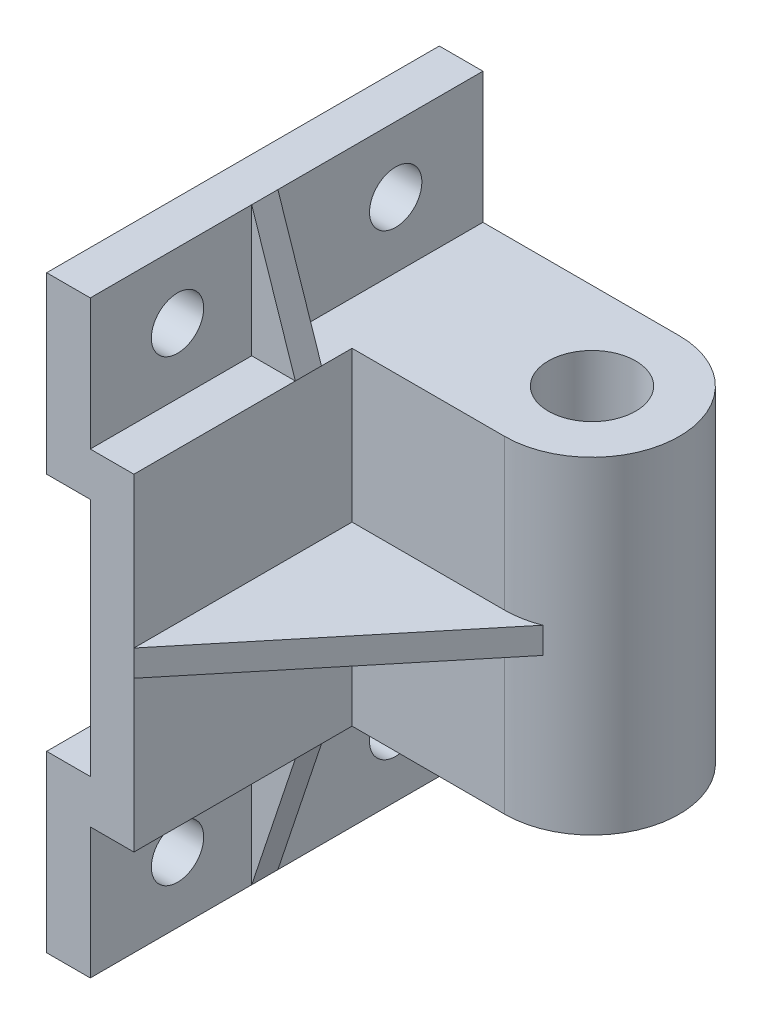
SolidWorks part; units mm, degrees
ref_plane "Ön Düzlem" through (0, 0, 0) normal (0, 0, 1) x (1, 0, 0)
ref_plane "Üst Düzlem" through (0, 0, 0) normal (0, 1, 0) x (1, 0, 0)
ref_plane "Sağ Düzlem" through (0, 0, 0) normal (1, 0, 0) x (0, 0, -1)
sketch "Çizim1" plane through (0, 0, 0) normal (0, 0, 1) x (1, 0, 0)
  line L2 (0, 0) -> (0, -75)
  line L4 (-10, -10) -> (-10, -65)
  line L7 (-10, -10) -> (-20, -10)
  line L9 (0, 0) -> (-10, 0)
  line L12 (-20, -10) -> (-20, 30)
  line L13 (-20, 30) -> (-10, 30)
  line L14 (-10, 0) -> (-10, 30)
  line L15 (-10, -65) -> (-20, -65)
  line L17 (0, -75) -> (-10, -75)
  line L20 (-20, -65) -> (-20, -105)
  line L21 (-20, -105) -> (-10, -105)
  line L22 (-10, -75) -> (-10, -105)
  point P0 (0, 0)
  point P2 (0, 0)
  point P8 (-40.7042, 0)
  point P12 (0, 0)
  point P13 (0, 0)
  point P18 (0, 0)
  point P19 (0, 0)
  point P20 (0, 0)
  point P21 (-10, 22.0605)
  point P22 (-20, -105.2649)
  dimension "D1" = 10
  dimension "D2" = 10
  dimension "D3" = 10
  dimension "D4" = 10
  dimension "D5" = 10
  dimension "D6" = 55
  dimension "D7" = 75
  dimension "D8" = 10
  dimension "D9" = 135
  dimension "D10" = 30
extrude "Yükseklik-Ekstrüzyon1" add sketch "Çizim1" against normal mid plane 90
sketch "Çizim2" plane through (0, 0, 0) normal (0, 1, 0) x (1, 0, 0)
  line L0 (0, 25) -> (35, 25) construction
  line L1 (0, 45) -> (35, 45)
  line L2 (0, 5) -> (35, 5)
  line L3 (-10, 45) -> (-10, -45) construction
  line L6 (0, 45) -> (0, -45) construction
  line L7 (0, 45) -> (0, 5)
  arc A1 (35, 5) -> (35, 45) centre (35, 25) ccw
  point P2 (18.7078, 23.4413)
  point P9 (0, 0)
  point P12 (35, 23.4413)
  point P13 (11.0631, 23.4413)
  point P14 (0, 0)
  point P15 (0, 25)
  point P16 (0, 0)
  point P17 (35, 3.4413)
  point P18 (35, 43.4413)
  point P19 (0, 39.2754)
  point P20 (0, 0)
  dimension "D2" = 20
  dimension "D1" = 45
  dimension "D3" = 40
extrude "Yükseklik-Ekstrüzyon2" add sketch "Çizim2" against normal up to surface (75 mm away) up to face at (-5, -75, 0)
sketch "Çizim3" plane through (0, 0, 0) normal (0, 1, 0) x (1, 0, 0)
  circle A0 centre (35, 25) radius 10
  dimension "D1" = 20
extrude "Kes-Ekstrüzyon1" cut sketch "Çizim3" against normal blind 75
sketch "Çizim4" plane through (-10, 0, 0) normal (1, 0, 0) x (0, 0, -1)
  line L0 (-45, 0) -> (-45, 30) construction
  line L1 (45, 0) -> (-45, 0) construction
  circle A0 centre (-25, 15) radius 6
  circle A1 centre (25, 15) radius 6
  point P6 (-25, 14.0431)
  point P9 (0, 0)
  dimension "D3" = 12
  dimension "D4" = 12
  dimension "D1" = 20
  dimension "D2" = 50
  dimension "D5" = 15
extrude "Kes-Ekstrüzyon2" cut sketch "Çizim4" against normal through all
ref_plane "Düzlem1" through (0, -37.5, 0) normal (0, 1, 0) x (1, 0, 0)
mirror "Aynalama1" about plane through (0, -37.5, 0) normal (0, 1, 0) of "Kes-Ekstrüzyon2"
ref_plane "Düzlem2" through (0, 0, 8) normal (0, 0, 1) x (1, 0, 0)
sketch "Çizim5" plane through (0, 0, 8) normal (0, 0, 1) x (1, 0, 0)
  line L0 (-10, 30) -> (0, 0)
  line L1 (0, 0) -> (-10, 0)
  line L2 (-10, 0) -> (-10, 30)
extrude "Yükseklik-Ekstrüzyon3" add sketch "Çizim5" against normal blind 6
mirror "Aynalama2" about plane through (0, -37.5, 0) normal (0, 1, 0) of "Yükseklik-Ekstrüzyon3"
sketch "Çizim6" plane through (0, -37.5, 0) normal (0, 1, 0) x (1, 0, 0)
  line L0 (0, 9.6267) -> (45, 9.6267)
  line L2 (45, 9.6267) -> (0, -45)
  line L3 (0, -8) -> (0, -45) construction
  line L4 (0, -45) -> (0, 9.6267)
  point P2 (0, 0)
  point P3 (0, 0)
  point P4 (0, -41.0821)
  point P5 (0, 0)
  point P9 (0, 0)
  point P10 (0, 0)
  point P11 (0, -45)
  dimension "D1" = 45
extrude "Yükseklik-Ekstrüzyon4" add sketch "Çizim6" along normal mid plane 6
